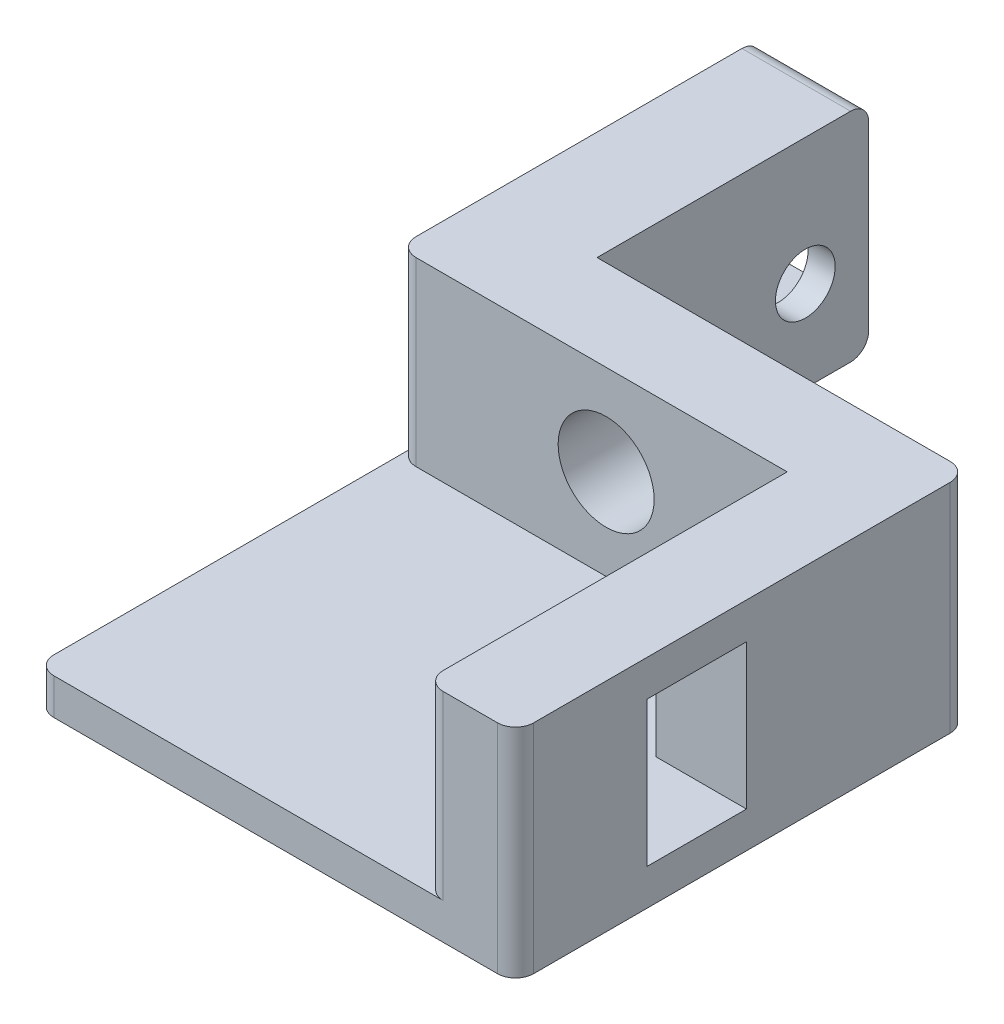
SolidWorks part; units mm, degrees
ref_plane "Plano frontal" through (0, 0, 0) normal (0, 0, 1) x (1, 0, 0)
ref_plane "Plano superior" through (0, 0, 0) normal (0, 1, 0) x (1, 0, 0)
ref_plane "Plano direito" through (0, 0, 0) normal (1, 0, 0) x (0, 0, -1)
sketch "Esboço1" plane through (0, 0, 0) normal (0, 1, 0) x (1, 0, 0)
  line L0 (0, 0) -> (0, 20)
  line L1 (0, 20) -> (6, 20)
  line L2 (6, 20) -> (6, 5)
  line L3 (6, 5) -> (26.5, 5)
  line L4 (26.5, 5) -> (26.5, -20)
  line L5 (26.5, -20) -> (21.5, -20)
  line L6 (21.5, -20) -> (21.5, 0)
  line L7 (21.5, 0) -> (0, 0)
  dimension "D1" = 20
  dimension "D2" = 25
  dimension "D3" = 6
  dimension "D4" = 5
  dimension "D5" = 5
  dimension "D7" = 20.5
extrude "Ressalto-extrusão1" add sketch "Esboço1" along normal blind 10 contours L0 L1 L2 L3 L4 L5 L6 L7
sketch "Esboço8" plane through (0, 0, 0) normal (0, -1, 0) x (1, 0, 0)
  line L1 (26.5, -5) -> (6, -5)
  line L2 (26.5, -5) -> (26.5, 20)
  line L3 (26.5, 20) -> (0, 20)
  line L4 (0, -20) -> (0, 20)
  line L5 (0, -20) -> (6, -20)
  line L8 (6, -20) -> (6, -5)
extrude "Ressalto-extrusão2" add sketch "Esboço8" along normal blind 2
sketch "Esboço2" plane through (21.5, 0, 0) normal (-1, 0, 0) x (0, 0, 1)
  line L1 (7.25, 0) -> (12.75, 0)
  line L2 (7.25, 0) -> (7.25, 8)
  line L3 (7.25, 8) -> (12.75, 8)
  line L4 (12.75, 0) -> (12.75, 8)
  line L5 (20, 10) -> (20, 0) construction
  line L6 (-5, -2) -> (20, -2) construction
  line L7 (-5, 10) -> (20, 10) construction
  dimension "D1" = 2
  dimension "D2" = 5.5
  dimension "D3" = 7.25
  dimension "D4" = 2
extrude "Corte-extrusão1" cut sketch "Esboço2" against normal blind 10
sketch "Esboço3" plane through (6, 0, 0) normal (1, 0, 0) x (0, 0, -1)
  line L0 (20, 10) -> (20, -2) construction
  line L1 (-20, -2) -> (20, -2) construction
  circle A0 centre (16.5, 3) radius 1.65
  dimension "D1" = 3.3
  dimension "D2" = 3.5
  dimension "D3" = 5
extrude "Corte-extrusão2" cut sketch "Esboço3" against normal blind 10
sketch "Esboço4" plane through (0, 0, -5) normal (0, 0, -1) x (-1, 0, 0)
  line L0 (-6, 10) -> (-6, -2) construction
  line L1 (-21.5, 10) -> (-21.5, 0) construction
  circle A0 centre (-11.5, 5) radius 2.65
  point P6 (-21.5, 5)
  dimension "D1" = 5.3
  dimension "D2" = 5.5
extrude "Corte-extrusão3" cut sketch "Esboço4" against normal blind 10
sketch "Esboço7" plane through (0, 0, 0) normal (-1, 0, 0) x (0, 0, 1)
  line L1 (-13.0359, 3) -> (-14.7679, 6)
  line L2 (-14.7679, 6) -> (-18.2321, 6)
  line L3 (-18.2321, 6) -> (-19.9641, 3) construction
  line L4 (-19.9641, 3) -> (-18.2321, 0) construction
  line L5 (-18.2321, 0) -> (-14.7679, 0)
  line L6 (-14.7679, 0) -> (-13.0359, 3)
  line L7 (-18.2321, 0) -> (-20, 0)
  line L8 (-20, 10) -> (-20, -2) construction
  line L9 (-20, 0) -> (-20, 6)
  line L10 (-20, 6) -> (-18.2321, 6)
  circle A0 centre (-16.5, 3) radius 3 construction
  dimension "D1" = 6
extrude "Corte-extrusão4" cut sketch "Esboço7" against normal blind 3 from offset 1.5 contours L6 L1 L2 L10 L9 L7 L5 offset against normal yes
fillet "Filete1" radius 1 7 edges at (0, -1, 20) (21.5, 5, 20) (26.5, 4, 20) (26.5, 4, -5) (0, 5, 0) (3, -2, -20) (3, 10, -20)
